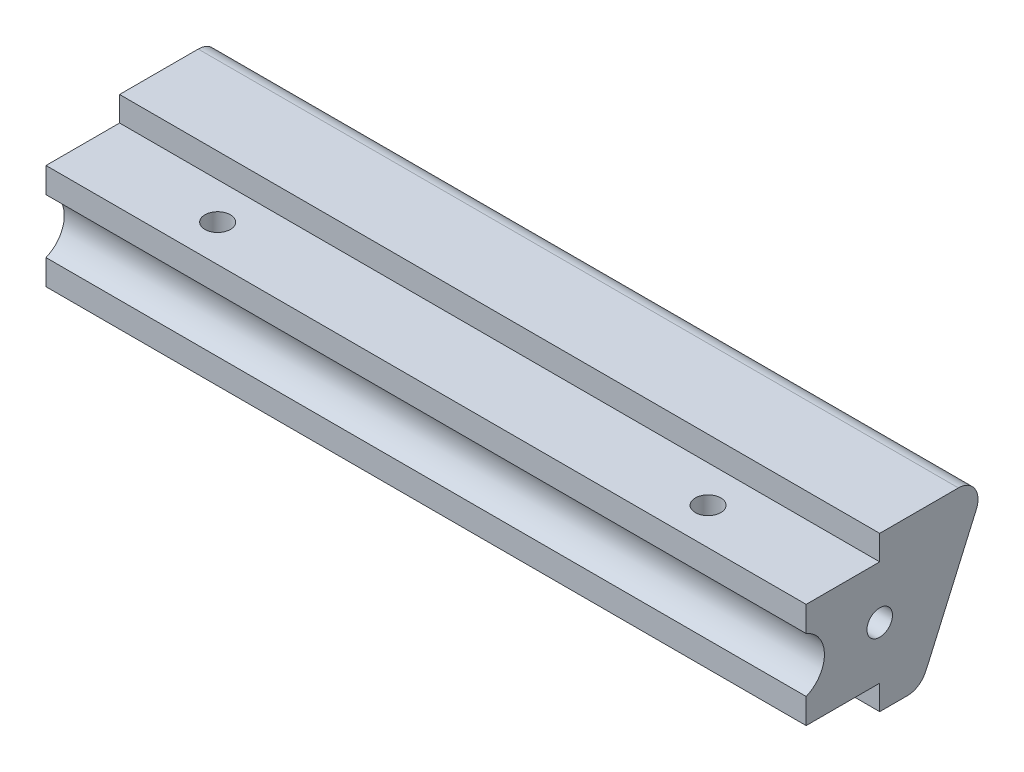
SolidWorks part; units mm, degrees
ref_plane "Front Plane" through (0, 0, 0) normal (0, 0, 1) x (1, 0, 0)
ref_plane "Top Plane" through (0, 0, 0) normal (0, 1, 0) x (1, 0, 0)
ref_plane "Right Plane" through (0, 0, 0) normal (1, 0, 0) x (0, 0, -1)
sketch "Sketch1" plane through (0, 0, 0) normal (1, 0, 0) x (0, 0, -1)
  line L0 (0, 16.7996) -> (0, 3.2004)
  line L1 (0, 20) -> (14.605, 20) construction
  line L2 (0, 20) -> (0, 0) construction
  line L3 (0, 0) -> (14.605, 0) construction
  line L4 (14.605, 20) -> (14.605, 0) construction
  line L5 (0, 20) -> (14.605, 20) construction
  line L6 (0, 20) -> (0, 16.7996) construction
  line L9 (0, 3.2004) -> (9.525, 3.2004)
  line L10 (0, 3.2004) -> (0, 0) construction
  line L11 (0, 0) -> (14.605, 0) construction
  line L14 (23.6039, 20) -> (15.8687, 2.3944)
  line L15 (14.605, 0) -> (9.525, 0)
  line L16 (9.525, 3.2004) -> (9.525, 0)
  line L17 (23.6039, 20) -> (9.525, 20)
  line L18 (9.525, 20) -> (9.525, 16.7996)
  line L19 (9.525, 16.7996) -> (0, 16.7996)
  arc A2 (15.8687, 2.3944) -> (14.605, 0) centre (-1.4419, 10) cw
  dimension "D4" = 9.525
  dimension "D5" = 18.9078
  dimension "D1" = 20
  dimension "D2" = 2.3944
  dimension "D3" = 3.2004
  dimension "D6" = 113.719
  dimension "D7" = 5.08
extrude "Boss-Extrude1" add sketch "Sketch1" along normal blind 98.425
sketch "Sketch4" plane through (0, 0, 0) normal (-1, 0, 0) x (0, 0, 1)
  line L1 (0, 13.5263) -> (0, 6.4737)
  line L2 (-19.2103, 10) -> (1.4427, 10) construction
  line L3 (0, 3.2004) -> (-9.525, 3.2004) construction
  line L4 (0, 16.7996) -> (0, 3.2004) construction
  line L5 (-15.8687, 2.3944) -> (-23.6039, 20) construction
  arc A0 (0, 13.5263) -> (0, 6.4737) centre (1.4427, 10) ccw
  point P3 (0, 10)
  dimension "D1" = 3.81
  dimension "D2" = 1.4427
extrude "Cut-Extrude2" cut sketch "Sketch4" against normal up to surface (98.425 mm away) up to face at (98.425, 9.1524, -10.2467)
sketch "Sketch5" plane through (0, 16.7996, 0) normal (0, 1, 0) x (1, 0, 0)
  line L0 (49.2125, 9.525) -> (49.2125, 0) construction
  line L1 (17.4625, 4.7625) -> (80.9625, 4.7625) construction
  line L2 (98.425, 9.525) -> (0, 9.525) construction
  line L3 (98.425, 0) -> (0, 0) construction
  circle A4 centre (17.4625, 4.7625) radius 1.651
  circle A5 centre (80.9625, 4.7625) radius 1.651
  point P8 (49.2125, 4.7625)
  dimension "D1" = 63.5
  dimension "D2" = 3.302
extrude "Cut-Extrude3" cut sketch "Sketch5" against normal up to surface (13.5992 mm away) up to face at (49.2125, 3.2004, -4.7625)
fillet "Fillet1" radius 2.54 2 edges at (49.2125, 0, -14.605) (49.2125, 20, -23.6039)
sketch "Sketch6" plane through (98.425, 0, 0) normal (1, 0, 0) x (0, 0, -1)
  line L0 (9.525, 16.7996) -> (9.525, 3.2004) construction
  circle A0 centre (9.525, 10) radius 1.651
  dimension "D1" = 3.302
extrude "Cut-Extrude4" cut sketch "Sketch6" against normal up to surface (98.425 mm away) up to face at (0, 9.271, -9.8284)
